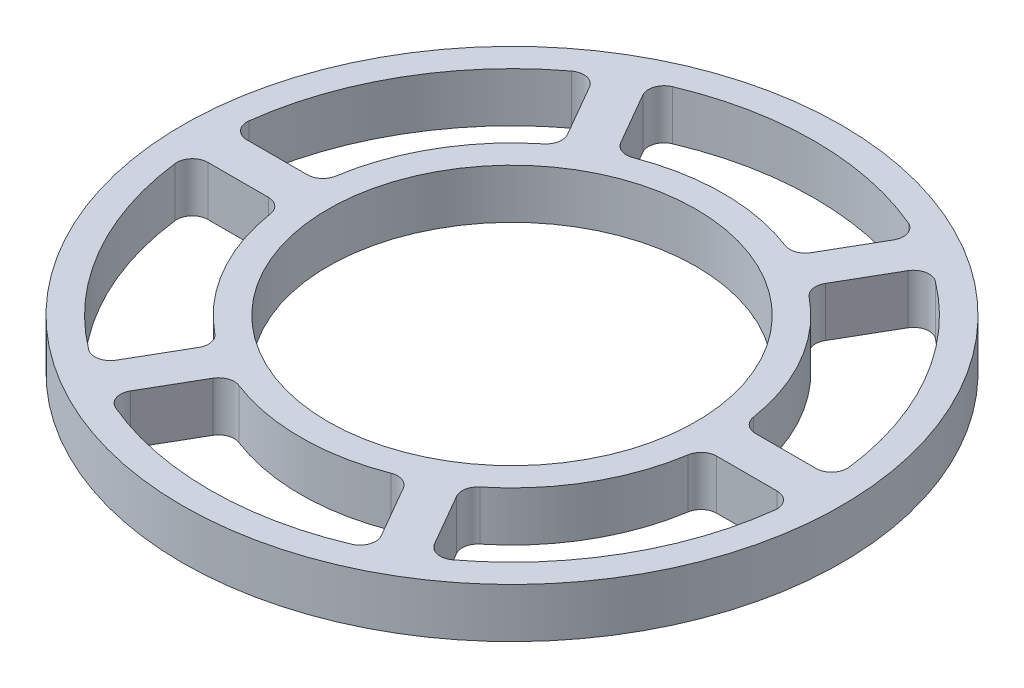
SolidWorks part; units mm, degrees
material "6061-T6 (SS)"
ref_plane "Front Plane" through (0, 0, 0) normal (0, 0, 1) x (1, 0, 0)
ref_plane "Top Plane" through (0, 0, 0) normal (0, 1, 0) x (1, 0, 0)
ref_plane "Right Plane" through (0, 0, 0) normal (1, 0, 0) x (0, 0, -1)
sketch "Sketch2" plane through (0, 0, 0) normal (1, 0, 0) x (0, 0, -1)
  line L0 (-49.2125, 0) -> (-82.55, 0)
  line L1 (-82.55, 0) -> (-82.55, 12.7)
  line L2 (-82.55, 12.7) -> (-49.2125, 12.7)
  line L3 (-49.2125, 12.7) -> (-49.2125, 0)
  dimension "D1" = 82.55
  dimension "D2" = 12.7
  dimension "D4" = 49.2125
ref_axis "Axis1" through (0, -0.5, 0) along (0, 1, 0)
revolve "Revolve1" add sketch "Sketch2" angle 360 about axis through (0, -0.5, 0) along (0, 1, 0)
hole_wizard "#6 (0.204) Diameter Hole1" [suppressed] positions "Sketch6" profile "Sketch7" hole size "#6" standard "ANSI Inch"
sketch "Sketch6" plane through (0, 12.7, 0) normal (0, 1, 0) x (1, 0, 0)
  line L0 (0, 0) -> (-69.8201, 120.932) construction
  line L2 (0, 0) -> (0, 109.0908) construction
  point P0 (-35, 60.6218)
  dimension "D1" = 30
  dimension "D2" = 70
sketch "Sketch7" plane through (-35, 12.7, -60.6218) normal (1, 0, 0) x (0, 0, 1)
  line L0 (0, 0) -> (0, 12.7)
  line L1 (0, 12.7) -> (2.5908, 12.7)
  line L2 (2.5908, 12.7) -> (2.5908, 0)
  line L5 (2.5908, 0) -> (0, 0)
  line L11 (0, -6.35) -> (0, 107.95) construction
  dimension "Thru Hole Dia." = 5.1816
  dimension "Thru Hole Depth" = 12.7
pattern_circular "CirPattern3" [suppressed] count 6 over 360 about axis through (0, -0.5, 0) along (0, 1, 0)
sketch "Sketch8" plane through (0, 12.7, 0) normal (0, 1, 0) x (1, 0, 0)
  line L4 (0, 0) -> (0, 93.9995) construction
  line L5 (-22.6606, 49.2493) -> (-34.3642, 69.5205)
  line L6 (22.6606, 49.2493) -> (34.3642, 69.5205)
  line L7 (0, 0) -> (-35, 60.6218) construction
  arc A0 (-22.6606, 49.2493) -> (22.6606, 49.2493) centre (0, 0) cw
  arc A1 (-34.3642, 69.5205) -> (34.3642, 69.5205) centre (0, 0) cw
  circle A2 centre (0, 0) radius 82.55 construction
  circle A4 centre (0, 0) radius 49.2125 construction
  dimension "D1" = 5
  dimension "D2" = 5
  dimension "D3" = 5
  dimension "D4" = 30
extrude "Cut-Extrude1" cut sketch "Sketch8" against normal through all
fillet "Fillet1" radius 4 4 edges at (-22.6606, 6.35, -49.2493) (22.6606, 6.35, -49.2493) (34.3642, 6.35, -69.5205) (-34.3642, 6.35, -69.5205)
pattern_circular "CirPattern4" count 6 over 360 about axis through (0, 0, 0) along (0, 1, 0) of "Cut-Extrude1", "Fillet1"
chamfer "Chamfer1" [suppressed] distance 1 angle 45
chamfer "Chamfer2" [suppressed] distance 1 angle 45
sketch "Sketch9" plane through (0, 0, 0) normal (0, 1, 0) x (1, 0, 0)
  circle A0 centre (0, 0) radius 49.2125
  circle A1 centre (0, 0) radius 47.2125
  circle A2 centre (0, 0) radius 49.2125 construction
  dimension "D1" = 2
extrude "Boss-Extrude1" add sketch "Sketch9" along normal blind 12.7
sketch "Sketch10" plane through (0, 0, 0) normal (0, 1, 0) x (1, 0, 0)
  circle A0 centre (0, 0) radius 84.55
  circle A1 centre (0, 0) radius 82.55
  circle A2 centre (0, 0) radius 82.55 construction
  dimension "D1" = 2
extrude "Boss-Extrude2" add sketch "Sketch10" along normal blind 12.7
equation "\"TubeDiameter\" = 6.500in"
equation "\"D1@Sketch2\"=\"TubeDiameter\"/2"
